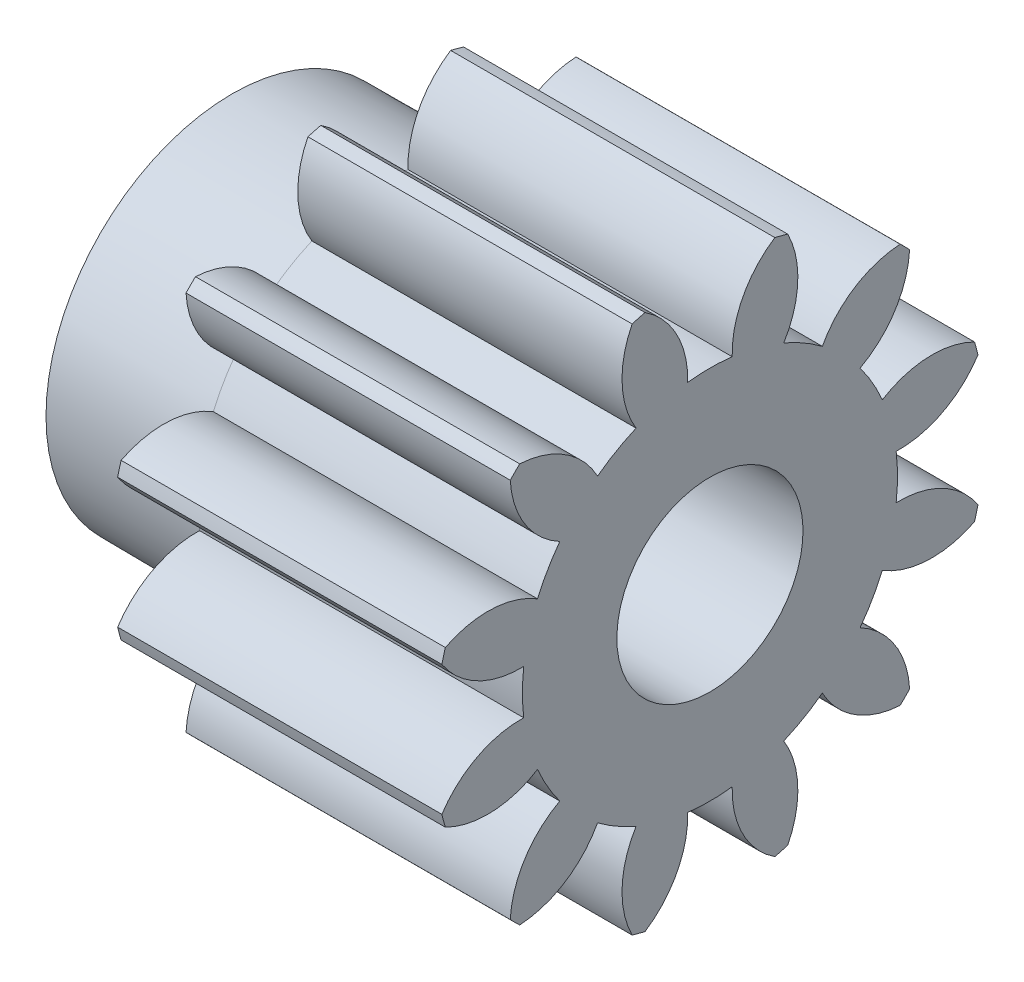
SolidWorks part; units mm, degrees
ref_plane "Plane1" through (0, 0, 0) normal (0, 0, 1) x (1, 0, 0)
ref_plane "Plane2" through (0, 0, 0) normal (0, 1, 0) x (1, 0, 0)
ref_plane "Plane3" through (0, 0, 0) normal (1, 0, 0) x (0, 0, -1)
sketch "HoldingSke" plane through (0, 0, 0) normal (0, 1, 0) x (1, 0, 0)
  line L0 (0, 0) -> (496.899, -105.6191)
  line L1 (-15, 0) -> (100, 0) construction
  line L2 (0, 0) -> (-2.1039, 2.3779)
  line L3 (0, 0) -> (-11.863, 4.5341)
  line L4 (0, 0) -> (8.4473, 1.7955)
  line L5 (0, 0) -> (-47.5972, -17.7524)
  line L6 (0, 0) -> (-10.5278, -7.1032)
  line L7 (-2.1039, 2.3779) -> (8.8308, 51.9871)
  line L8 (-76.2, 54.61) -> (-69.596, 54.61)
  line L9 (-71.009, 38.7566) -> (-53.1078, 45.2721)
  line L10 (-76.2, 71.12) -> (104.1128, 71.12)
  line L11 (0, 0) -> (-12.7, 0)
  line L12 (-76.2, 101.6) -> (-76.1492, 101.6)
  line L13 (24.9733, 27.94) -> (52.9518, 28.4284)
  line L14 (24.9733, 27.94) -> (25.0241, 27.9398)
  line L15 (24.9733, 27.94) -> (100.4021, 29.52)
  circle A0 centre (0, 0) radius 3.175
  circle A1 centre (0, 0) radius 6.0452
  circle A2 centre (0, 0) radius 38.1
  circle A3 centre (0, 0) radius 3.175
  dimension "MHD" = 12.0904
  dimension "Hub_dia" = 76.2
  dimension "Bore" = 6.35
  dimension "MBD" = 6.35
  dimension "Num_teeth" = 12
  dimension "Pitch" = 508
  dimension "Overall_len" = 50.8
  dimension "Show_teeth" = 12
  dimension "Thickness" = 12.7
  dimension "OAL" = 50.8001
  dimension "T_dim" = 6.604
  dimension "Ap" = 20
  dimension "H" = 19.05
  dimension "Pitch_radius" = 180.3128
  dimension "Width" = 12.7
  dimension "Backlash" = 0.0508
  dimension "Addendum_fac" = 1
  dimension "Dedendum_fac" = 1.2
  dimension "Clearance_fac" = 0.2
  dimension "Dedendum_add" = 0.0508
sketch "BasProSke" plane through (0, 0, 0) normal (0, 1, 0) x (1, 0, 0)
  line L0 (-10, 0) -> (60, 0) construction
  line L1 (0, 0) -> (0, 8.89)
  line L2 (0, 0) -> (12.7, 0)
  line L3 (12.7, 0) -> (12.7, 8.89)
  line L4 (12.7, 8.89) -> (0, 8.89)
  dimension "Thickness" = 12.7
  dimension "Diameter" = 17.78
revolve "Base-Revolve" add sketch "BasProSke" angle 360 about L0
sketch "TooCutSke" plane through (0, 0, 0) normal (1, 0, 0) x (0, 0, -1)
  line L1 (0, 0) -> (0, 107) construction
  line L2 (0, 0) -> (-1.0834, 7.5426) construction
  line L3 (0, 0) -> (-3.9164, 14.6164) construction
  line L4 (-1.0834, 7.5426) -> (-1.9582, 7.3082) construction
  arc A0 (0.7171, 6.0025) -> (-0.7171, 6.0025) centre (0, 0) ccw
  arc A1 (2.1216, 8.6593) -> (-2.1216, 8.6593) centre (0, 0) ccw
  circle A2 centre (0, 0) radius 7.62 construction
  circle A3 centre (0, 0) radius 7.1605 construction
  arc A4 (-0.7171, 6.0025) -> (-2.1216, 8.6593) centre (-3.7638, 6.0915) ccw
  arc A5 (2.1216, 8.6593) -> (0.7171, 6.0025) centre (3.7638, 6.0915) ccw
  dimension "Root_dia" = 12.0904
  dimension "Overcut_dia" = 17.8308
  dimension "Pitch_dia" = 15.24
  dimension "Base_dia" = 14.3209
  dimension "Flank_rad" = 3.048
  dimension "Half_ang" = 15
  dimension "Half_CT" = 0.9057
extrude "ToothCut" cut sketch "TooCutSke" along normal through all
fillet "Breaks" [suppressed] radius 0.0254
fillet "RootFillets" [suppressed] radius 0.3048
pattern_circular "TeethCuts" count 12 every 30 about axis through (-10, 0, 0) along (1, 0, 0) of "ToothCut", "RootFillets", "Breaks"
sketch "HubNeaOneSke" plane through (0, 0, 0) normal (-1, 0, 0) x (0, 0, 1)
  circle A0 centre (0, 0) radius 6.0452
  dimension "Diameter" = 12.0904
extrude "HubNearOne" [suppressed] add sketch "HubNeaOneSke" along normal blind 38.1001
sketch "HubNeaBotSke" plane through (0, 0, 0) normal (-1, 0, 0) x (0, 0, 1)
  circle A0 centre (0, 0) radius 6.0452
  dimension "Diameter" = 12.0904
extrude "HubNearBoth" [suppressed] add sketch "HubNeaBotSke" along normal blind 19.05
ref_plane "FarPln" through (12.7, 0, 0) normal (1, 0, 0) x (0, 0, -1)
sketch "HubFarSke" plane through (12.7, 0, 0) normal (1, 0, 0) x (0, 0, -1)
  circle A0 centre (0, 0) radius 6.0452
  dimension "Diameter" = 12.0904
extrude "HubFar" [suppressed] add sketch "HubFarSke" along normal blind 19.05
sketch "BorSke" plane through (0, 0, 0) normal (1, 0, 0) x (0, 0, -1)
  circle A0 centre (0, 0) radius 3
  dimension "D1" = 6
extrude "Bore" cut sketch "BorSke" along normal mid plane 101.6001
sketch "KeySke" plane through (0, 0, 0) normal (1, 0, 0) x (0, 0, -1)
  line L0 (-0.127, 0) -> (-0.127, 3.429)
  line L1 (-0.127, 3.429) -> (0.127, 3.429)
  line L2 (0.127, 3.429) -> (0.127, 0)
  line L3 (0, 0) -> (0, 34) construction
  line L4 (-0.127, 0) -> (0.127, 0)
  dimension "Offset" = 3.429
  dimension "Width" = 0.254
extrude "Keyway" [suppressed] cut sketch "KeySke" along normal mid plane 101.6001
pattern_circular "Keyway2" [suppressed] count 2 every 90 about axis through (-10, 0, 0) along (1, 0, 0)
sketch "Sketch1" plane through (0, 0, 0) normal (0, 0, 1) x (1, 0, 0)
  line L0 (0, 0) -> (-2.5422, 0) construction
  line L1 (0, -4) -> (-4.95, -4)
  line L2 (-4.95, -4) -> (-4.95, -6)
  line L3 (-4.95, -6) -> (0, -6.0452)
  line L4 (0, -6.0452) -> (0, -4)
  dimension "D1" = 2
  dimension "D2" = 4
  dimension "D3" = 4.95
revolve "Revolve1" add sketch "Sketch1" angle 360 about L0
sketch "Sketch2" plane through (0, 0, 0) normal (0, 0, 1) x (1, 0, 0)
  line L0 (12.7, -8.6403) -> (0, -8.6403) construction
  line L1 (12.7, 8.6403) -> (10.45, 8.6403)
  line L2 (12.7, 8.6403) -> (12.7, -8.6403)
  line L3 (12.7, -8.6403) -> (10.45, -8.6403)
  line L4 (10.45, 8.6403) -> (10.45, -8.6403)
  dimension "D1" = 2.25
extrude "Cut-Extrude1" cut sketch "Sketch2" against normal through all both and the other way through all
equation "' \"Pitch@HoldingSke\" = 4"
equation "' \"Num_teeth@HoldingSke\" = 12"
equation "' \"Ap@HoldingSke\" =  20"
equation "' \"Ap@HoldingSke\" = 20"
equation "' \"Width@HoldingSke\" = 0.5"
equation "' \"Hub_dia@HoldingSke\"= 1"
equation "' \"Hub_dia@HoldingSke\" = 1"
equation "' \"Overall_len@HoldingSke\" = 1.0"
equation "' \"Bore@HoldingSke\" = 0.75"
equation "' \"T_dim@HoldingSke\" = 0.85"
equation "' \"Width@KeySke\" = 0.25"
equation "' \"Show_teeth@HoldingSke\" = 13"
equation "' \"Backlash@HoldingSke\" = 0.009"
equation "' \"Addendum_fac@HoldingSke\" = 1.0"
equation "' \"Dedendum_fac@HoldingSke\" = 1.25"
equation "' \"Dedendum_add@HoldingSke\" = 0.00005"
equation "' \"Clearance_fac@HoldingSke\" = 0.25"
equation "' \"Pitch@HoldingSke\" = 0.5"
equation "' \"Num_teeth@HoldingSke\" = 23"
equation "' \"Show_teeth@HoldingSke\" = 23"
equation "' \"Backlash@HoldingSke\" = 0.0375"
equation "\"Overcut_dia@TooCutSke\" = (\"Num_teeth@HoldingSke\" + 2 * \"Addendum_fac@HoldingSke\") / \"Pitch@HoldingSke\" + 0.002"
equation "\"Pitch_dia@TooCutSke\" = \"Num_teeth@HoldingSke\" / \"Pitch@HoldingSke\""
equation "\"Base_dia@TooCutSke\" = \"Num_teeth@HoldingSke\" / \"Pitch@HoldingSke\" * cos((\"Ap@HoldingSke\"  * 3.14159265 / 180))"
equation "\"Root_dia@TooCutSke\" = (\"Num_teeth@HoldingSke\" + 2) / \"Pitch@HoldingSke\" - 2 * (\"Addendum_fac@HoldingSke\" + \"Dedendum_fac@HoldingSke\") / \"Pitch@HoldingSke\" - \"Dedendum_add@HoldingSke\" * 2"
equation "\"Half_ang@TooCutSke\" = 180 / \"Num_teeth@HoldingSke\""
equation "\"Half_CT@TooCutSke\" = \"Num_teeth@HoldingSke\" / \"Pitch@HoldingSke\" * sin((3.14159265 / 2 / \"Num_teeth@HoldingSke\")) / 2 - 7 * \"Backlash@HoldingSke\" / 4"
equation "\"Flank_rad@TooCutSke\" = \"Num_teeth@HoldingSke\" / \"Pitch@HoldingSke\" / 5"
equation "\"Radius@RootFillets\" = \"Clearance_fac@HoldingSke\" / \"Pitch@HoldingSke\" + \"Dedendum_add@HoldingSke\""
equation "\"Break_rad@Breaks\" = 0.02 / \"Pitch@HoldingSke\""
equation "\"Thickness@HoldingSke\" = \"Width@HoldingSke\""
equation "\"OAL@HoldingSke\" = \"Thickness@HoldingSke\""
equation "\"MHD@HoldingSke\" = (\"Num_teeth@HoldingSke\" + 2) / \"Pitch@HoldingSke\" - 2 * (\"Addendum_fac@HoldingSke\" + \"Dedendum_fac@HoldingSke\")  / \"Pitch@HoldingSke\" - \"Dedendum_add@HoldingSke\" * 2"
equation "\"MBD@HoldingSke\" = (\"Num_teeth@HoldingSke\" + 2) / \"Pitch@HoldingSke\" - 2 * (\"Addendum_fac@HoldingSke\" + \"Dedendum_fac@HoldingSke\")  / \"Pitch@HoldingSke\" - \"Dedendum_add@HoldingSke\" * 2 - 0.002"
equation "\"MHD@HoldingSke\" = ((sgn( \"MHD@HoldingSke\" - \"Hub_dia@HoldingSke\" )-1)*( \"MHD@HoldingSke\" - \"Hub_dia@HoldingSke\" ))/-2+ \"Hub_dia@HoldingSke\""
equation "\"MBD@HoldingSke\" = ((sgn( \"MBD@HoldingSke\" - \"Bore@HoldingSke\" )-1)*( \"MBD@HoldingSke\" - \"Bore@HoldingSke\" ))/-2+ \"Bore@HoldingSke\""
equation "\"OAL@HoldingSke\" = ((sgn( \"OAL@HoldingSke\" - \"Overall_len@HoldingSke\" )+1)*( \"OAL@HoldingSke\" - \"Overall_len@HoldingSke\" ))/2 + \"Overall_len@HoldingSke\" + 0.000002"
equation "\"Num_teeth@TeethCuts\" = int( \"Show_teeth@HoldingSke\" ) + 1"
equation "\"Num_teeth@TeethCuts\" = ((sgn( \"Num_teeth@TeethCuts\" - \"Num_teeth@HoldingSke\" )-1)*( \"Num_teeth@TeethCuts\" - \"Num_teeth@HoldingSke\" ))/-2+ \"Num_teeth@HoldingSke\""
equation "\"Num_teeth@TeethCuts\" = ((sgn( \"Num_teeth@TeethCuts\" - 2.0)+1)*( \"Num_teeth@TeethCuts\" - 2.0))/2 +2.0"
equation "\"Angle@TeethCuts\" = 360.0 / \"Num_teeth@HoldingSke\""
equation "\"Diameter@BasProSke\" = (\"Num_teeth@HoldingSke\" + 2 * \"Addendum_fac@HoldingSke\") / \"Pitch@HoldingSke\""
equation "\"Thickness@BasProSke\"  = \"Thickness@HoldingSke\""
equation "' \"Fillet_rad@BasProSke\" =  \"Thickness@HoldingSke\" * 0.05"
equation "' \"Fillet_rad@BasProSke\" = \"Thickness@HoldingSke\" * 0.05"
equation "\"MHD@HoldingSke\" = ((sgn( \"MHD@HoldingSke\" - \"Root_dia@TooCutSke\" )-1)*( \"MHD@HoldingSke\" - \"Root_dia@TooCutSke\" ))/-2+ \"Root_dia@TooCutSke\""
equation "\"Diameter@HubNeaOneSke\" = \"MHD@HoldingSke\""
equation "\"Length@HubNearOne\" = \"OAL@HoldingSke\" - \"Thickness@BasProSke\""
equation "\"Diameter@HubNeaBotSke\" = \"MHD@HoldingSke\""
equation "\"Length@HubNearBoth\" = ( \"OAL@HoldingSke\" - \"Thickness@BasProSke\" ) / 2.0"
equation "\"Thickness@FarPln\" = \"Thickness@BasProSke\""
equation "\"Diameter@HubFarSke\" = \"MHD@HoldingSke\""
equation "\"Length@HubFar\" = ( \"OAL@HoldingSke\" - \"Thickness@BasProSke\" ) / 2.0"
equation "\"D1@Bore\" = \"OAL@HoldingSke\" * 2.0"
equation "\"D1@Keyway\" = \"OAL@HoldingSke\" * 2.0"
equation "\"Offset@KeySke\" = \"T_dim@HoldingSke\" - \"MBD@HoldingSke\" / 2.0"
